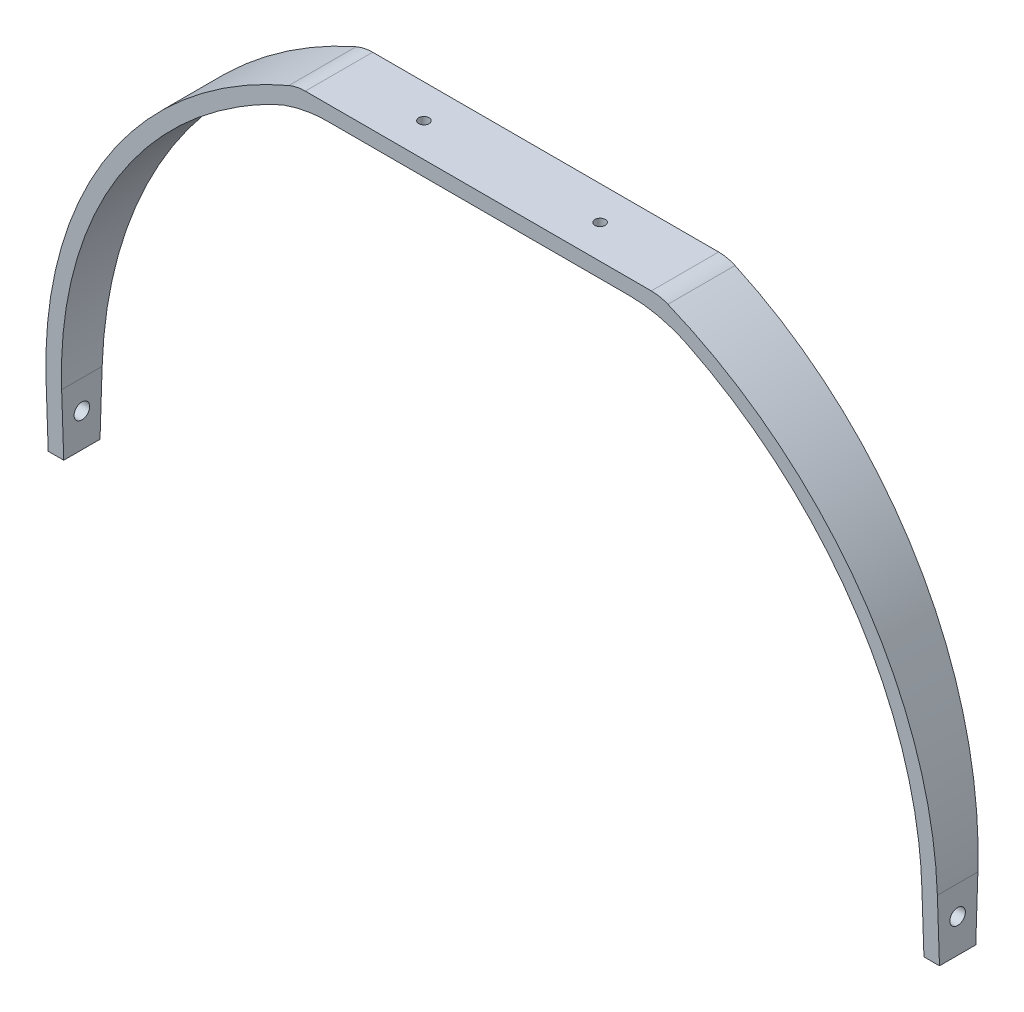
SolidWorks part; units mm, degrees
material "Thornel Mat VMA"
ref_plane "Front Plane" through (0, 0, 0) normal (0, 0, 1) x (1, 0, 0)
ref_plane "Top Plane" through (0, 0, 0) normal (0, 1, 0) x (1, 0, 0)
ref_plane "Right Plane" through (0, 0, 0) normal (1, 0, 0) x (0, 0, -1)
sketch "Sketch2" plane through (0, 0, 0) normal (0, 0, 1) x (1, 0, 0)
  line L0 (0, 236.3056) -> (0, -167.0502) construction
  line L1 (-273.05, 0) -> (-273.05, 38.1)
  line L2 (-111.125, 279.4) -> (0, 279.4)
  line L3 (-263.525, 0) -> (-263.525, 38.1)
  line L4 (-109.2319, 269.875) -> (0, 269.875)
  line L5 (-273.05, 0) -> (-263.525, 0)
  line L7 (109.2319, 269.875) -> (0, 269.875)
  line L8 (263.525, 0) -> (263.525, 38.1)
  line L9 (273.05, 0) -> (263.525, 0)
  line L10 (273.05, 0) -> (273.05, 38.1)
  line L11 (111.125, 279.4) -> (0, 279.4)
  arc A0 (-273.05, 38.1) -> (-111.125, 279.4) centre (-12.2953, 38.1) cw
  arc A1 (-263.525, 38.1) -> (-109.2319, 269.875) centre (-12.2953, 38.1) cw
  arc A2 (263.525, 38.1) -> (109.2319, 269.875) centre (12.2953, 38.1) ccw
  arc A3 (273.05, 38.1) -> (111.125, 279.4) centre (12.2953, 38.1) ccw
  dimension "D1" = 111.125
  dimension "D2" = 38.1
  dimension "D3" = 273.05
  dimension "D5" = 279.4
  dimension "D4" = 9.525
extrude "Boss-Extrude1" add sketch "Sketch2" along normal blind 41.275
sketch "Sketch3" plane through (273.05, 0, 0) normal (1, 0, 0) x (0, 0, -1)
  line L0 (-20.6375, 0) -> (-20.6375, 279.4) construction
  line L1 (-41.275, 279.4) -> (0, 279.4) construction
  line L2 (0, 0) -> (-9.525, 0)
  line L3 (-20.6375, 0) -> (-31.75, 0)
  line L4 (-41.275, 0) -> (0, 0) construction
  line L5 (-31.75, 0) -> (-41.275, 279.4)
  line L6 (-41.275, 279.4) -> (-41.275, 0)
  line L7 (-41.275, 0) -> (-31.75, 0)
  line L8 (0, 279.4) -> (0, 0)
  line L9 (-9.525, 0) -> (0, 279.4)
  circle A0 centre (-20.6375, 20.6375) radius 4.7625
  point P3 (-20.6375, 0)
  dimension "D2" = 9.525
  dimension "D1" = 11.1125
  dimension "D3" = 15.875
extrude "Cut-Extrude1" cut sketch "Sketch3" against normal through all contours L5 L6 L7 | L9 L8 L2 | A0
fillet "Fillet2" radius 76.2 2 edges at (109.2319, 269.875, 20.6375) (-109.2319, 269.875, 20.6375)
fillet "Fillet3" radius 25.4 2 edges at (111.125, 279.4, 20.6375) (-111.125, 279.4, 20.6375)
sketch "Sketch7" plane through (0, 279.4, 0) normal (0, 1, 0) x (1, 0, 0)
  line L0 (0, 30.71) -> (0, -80.1796) construction
  line L1 (-105.9917, -20.6375) -> (105.9917, -20.6375) construction
  line L2 (-105.9917, 0) -> (-105.9917, -41.275) construction
  line L3 (105.9917, -41.275) -> (105.9917, 0) construction
  circle A0 centre (-53.975, -20.6375) radius 3.175
  circle A1 centre (53.975, -20.6375) radius 3.175
  dimension "D1" = 6.35
  dimension "D2" = 50.8
extrude "Cut-Extrude2" cut sketch "Sketch7" against normal up to surface (9.525 mm away) up to face at (0, 269.875, 20.6375)
